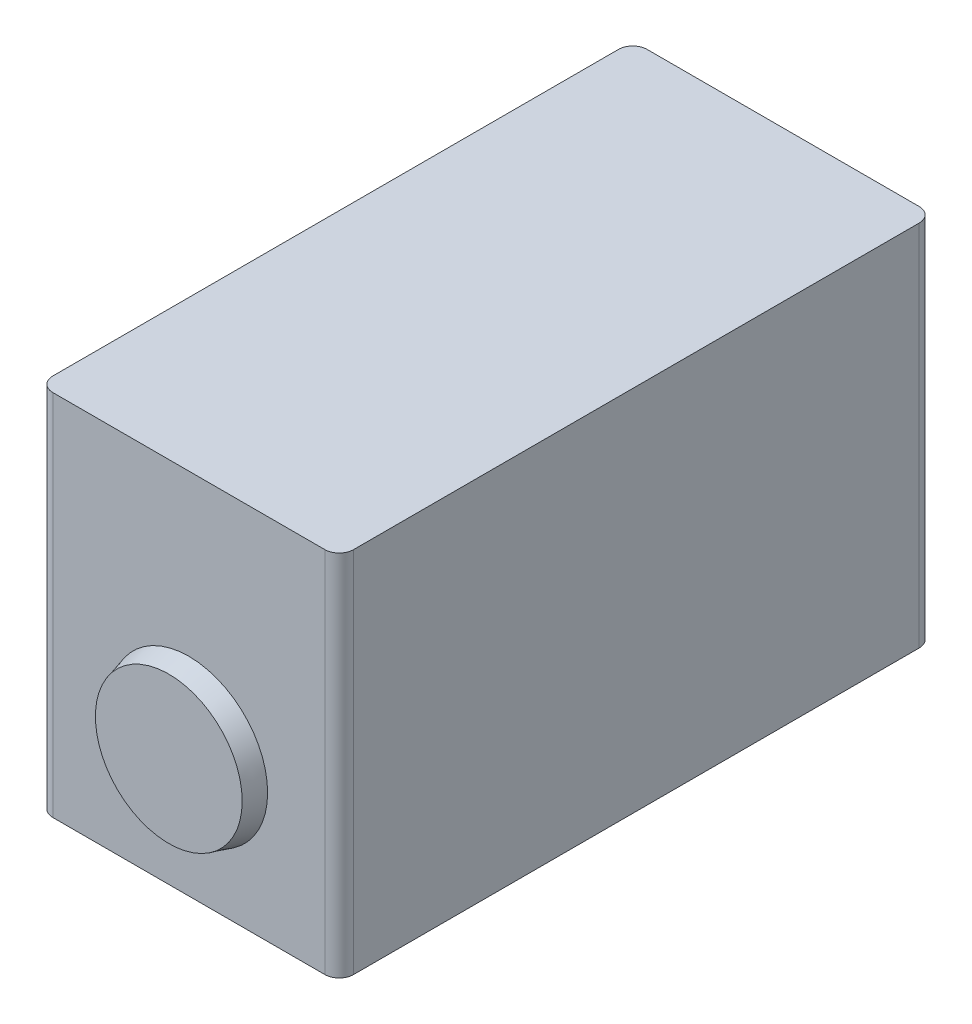
SolidWorks part; units mm, degrees
material "Magnesium Alloy"
ref_plane "Front Plane" through (0, 0, 0) normal (0, 0, 1) x (1, 0, 0)
ref_plane "Top Plane" through (0, 0, 0) normal (0, 1, 0) x (1, 0, 0)
ref_plane "Right Plane" through (0, 0, 0) normal (1, 0, 0) x (0, 0, -1)
sketch "Sketch1" plane through (0, 0, 0) normal (0, 1, 0) x (1, 0, 0)
  line L0 (10.5, -20.75) -> (-10.5, -20.75)
  line L1 (10.5, -20.75) -> (10.5, 20.75)
  line L2 (10.5, 20.75) -> (-10.5, 20.75)
  line L3 (-10.5, -20.75) -> (-10.5, 20.75)
  line L4 (10.5, -20.75) -> (-10.5, 20.75) construction
  line L5 (10.5, 20.75) -> (-10.5, -20.75) construction
  point P0 (0, 0)
  dimension "D1" = 21
  dimension "D2" = 41.5
extrude "Boss-Extrude1" add sketch "Sketch1" along normal blind 25.7
fillet "Fillet1" radius 1 4 edges at (-10.5, 12.85, -20.75) (10.5, 12.85, -20.75) (-10.5, 12.85, 20.75) (10.5, 12.85, 20.75)
sketch "Sketch2" plane through (0, 0, 20.75) normal (0, 0, 1) x (1, 0, 0)
  line L0 (-9.5, 0) -> (9.5, 0) construction
  circle A0 centre (0, 9) radius 5.5
  point P2 (0, 0)
  dimension "D1" = 11
  dimension "D2" = 9
extrude "Boss-Extrude2" add sketch "Sketch2" along normal blind 1.4 draft 15
